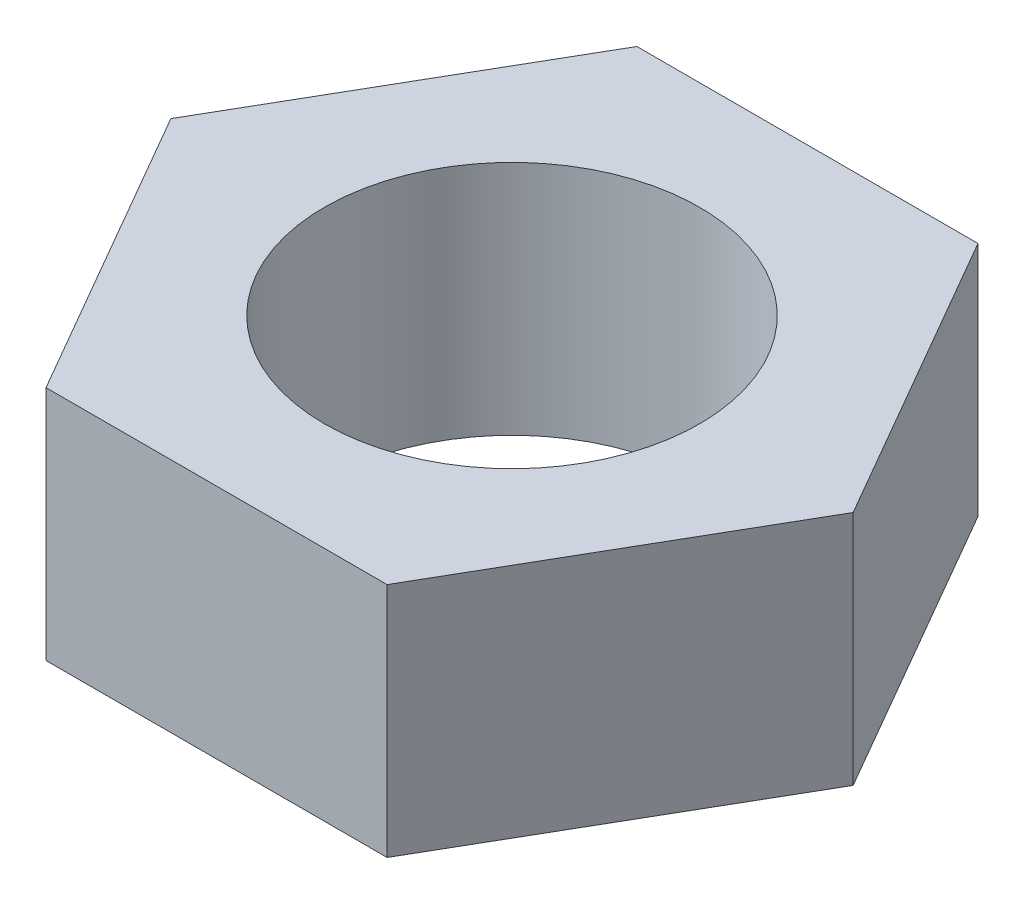
SolidWorks part; units mm, degrees
ref_plane "Alzado" through (0, 0, 0) normal (0, 0, 1) x (1, 0, 0)
ref_plane "Planta" through (0, 0, 0) normal (0, 1, 0) x (1, 0, 0)
ref_plane "Vista lateral" through (0, 0, 0) normal (1, 0, 0) x (0, 0, -1)
sketch "Croquis1" plane through (0, 0, 0) normal (0, 1, 0) x (1, 0, 0)
  line L1 (-34.641, 0) -> (-17.3205, -30)
  line L2 (-17.3205, -30) -> (17.3205, -30)
  line L3 (17.3205, -30) -> (34.641, 0)
  line L4 (34.641, 0) -> (17.3205, 30)
  line L5 (17.3205, 30) -> (-17.3205, 30)
  line L6 (-17.3205, 30) -> (-34.641, 0)
  circle A0 centre (0, 0) radius 19.05
  circle A1 centre (0, 0) radius 30 construction
  dimension "D1" = 38.1
  dimension "D2" = 60
extrude "Saliente-Extruir1" add sketch "Croquis1" along normal blind 24
